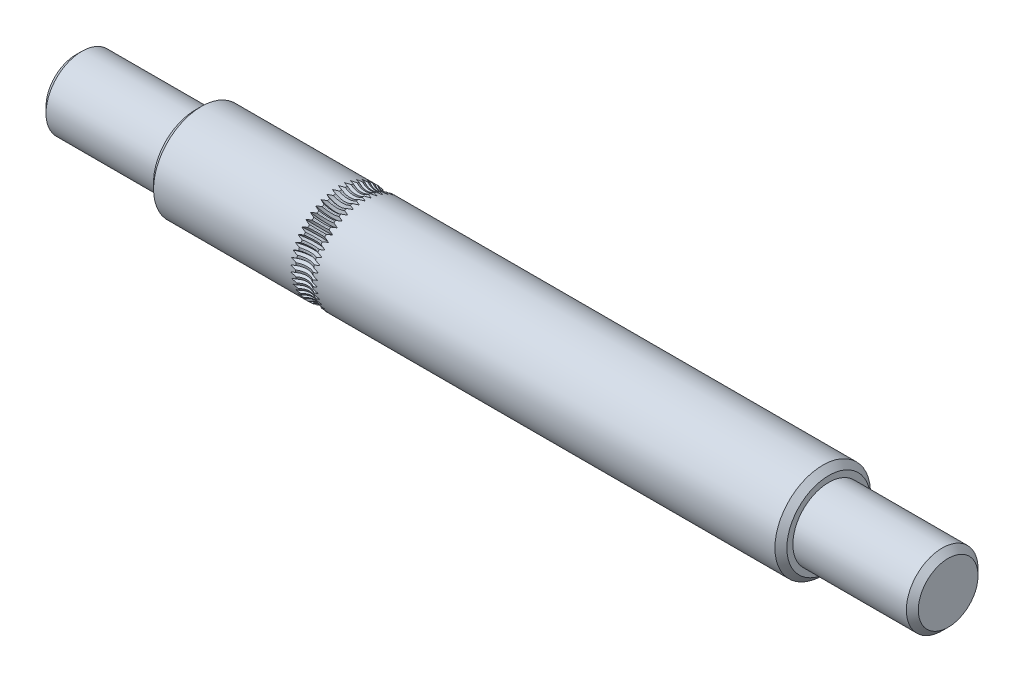
SolidWorks part; units mm, degrees
material "Plain Carbon Steel"
ref_plane "Front Plane" through (0, 0, 0) normal (0, 0, 1) x (1, 0, 0)
ref_plane "Top Plane" through (0, 0, 0) normal (0, 1, 0) x (1, 0, 0)
ref_plane "Right Plane" through (0, 0, 0) normal (1, 0, 0) x (0, 0, -1)
sketch "Sketch1" plane through (0, 0, 0) normal (0, 0, 1) x (1, 0, 0)
  line L0 (-13.1, 4) -> (39.9, 4)
  line L1 (-13.1, 3) -> (-23.1, 3)
  line L2 (-23.1, 0) -> (49.9, 0)
  line L3 (-13.1, 3) -> (-13.1, 4)
  line L4 (-23.1, 3) -> (-23.1, 0)
  line L5 (49.9, 0) -> (49.9, 3)
  line L6 (39.9, 4) -> (39.9, 3)
  line L7 (39.9, 3) -> (49.9, 3)
  line L8 (0, 0) -> (67.2135, 0) construction
  line L9 (0, 0) -> (0, 19.6593) construction
  dimension "D1" = 8
  dimension "D2" = 53
  dimension "D3" = 13.1
  dimension "D4" = 10
  dimension "D5" = 6
  dimension "D6" = 10
revolve "Revolve1" add sketch "Sketch1" angle 360 about L8
chamfer "Chamfer1" distance 0.5 angle 45 4 edges at (49.9, 0, 3) (39.9, 0, 4) (-13.1, 0, 4) (-23.1, 0, 3)
sketch "Sketch2" plane through (0, 0, 0) normal (1, 0, 0) x (0, 0, -1)
  line L0 (0, 0) -> (0, 5) construction
  line L1 (9.9899, 5) -> (-9.864, 5) construction
  line L2 (0.1562, 3.7705) -> (0, 3.5)
  line L3 (0, 3.5) -> (-0.1562, 3.7705)
  line L4 (-1.3354, 5) -> (1.3354, 5)
  line L5 (-0.1562, 3.7705) -> (-1.3354, 3.7705)
  line L6 (0.1562, 3.7705) -> (1.3354, 3.7705)
  line L7 (1.3354, 3.7705) -> (1.3354, 5)
  line L8 (-1.3354, 3.7705) -> (-1.3354, 5)
  line L9 (0, 0) -> (-6.9817, 0) construction
  line L10 (5.645, 4) -> (-5.97, 4) construction
  circle A0 centre (0, 0) radius 4 construction
  circle A1 centre (0, 0) radius 3.5 construction
  dimension "D5" = 5
  dimension "D1" = 60
  dimension "D2" = 3
  dimension "D3" = 2.459
  dimension "D4" = 1
revolve "Cut-Revolve1" cut sketch "Sketch2" angle 360 about L1
pattern_circular "CirPattern1" count 50 over 360 about axis through (0, 0, 0) along (-1, 0, 0) of "Cut-Revolve1"
sketch "Sketch3" plane through (0, 0, 0) normal (0, 0, 1) x (1, 0, 0)
  line L0 (49.4, 3) -> (39.9, 3) construction
  line L1 (8, 4) -> (0.75, 4)
  line L2 (8, 4) -> (8, 3)
  line L3 (8, 3) -> (0.75, 3)
  line L4 (0.75, 4) -> (0.75, 3)
  line L5 (-0.75, 4) -> (-8, 4)
  line L6 (-0.75, 4) -> (-0.75, 3)
  line L7 (-0.75, 3) -> (-8, 3)
  line L8 (-8, 4) -> (-8, 3)
  line L9 (0, 0) -> (0, 15.3026) construction
  line L10 (0, 0) -> (-13.7134, 0) construction
  line L11 (39.4, 4) -> (1.118, 4) construction
  dimension "D1" = 1.5
  dimension "D2" = 16
revolve "Cut-Revolve2" [suppressed] cut sketch "Sketch3" angle 360 about L10
